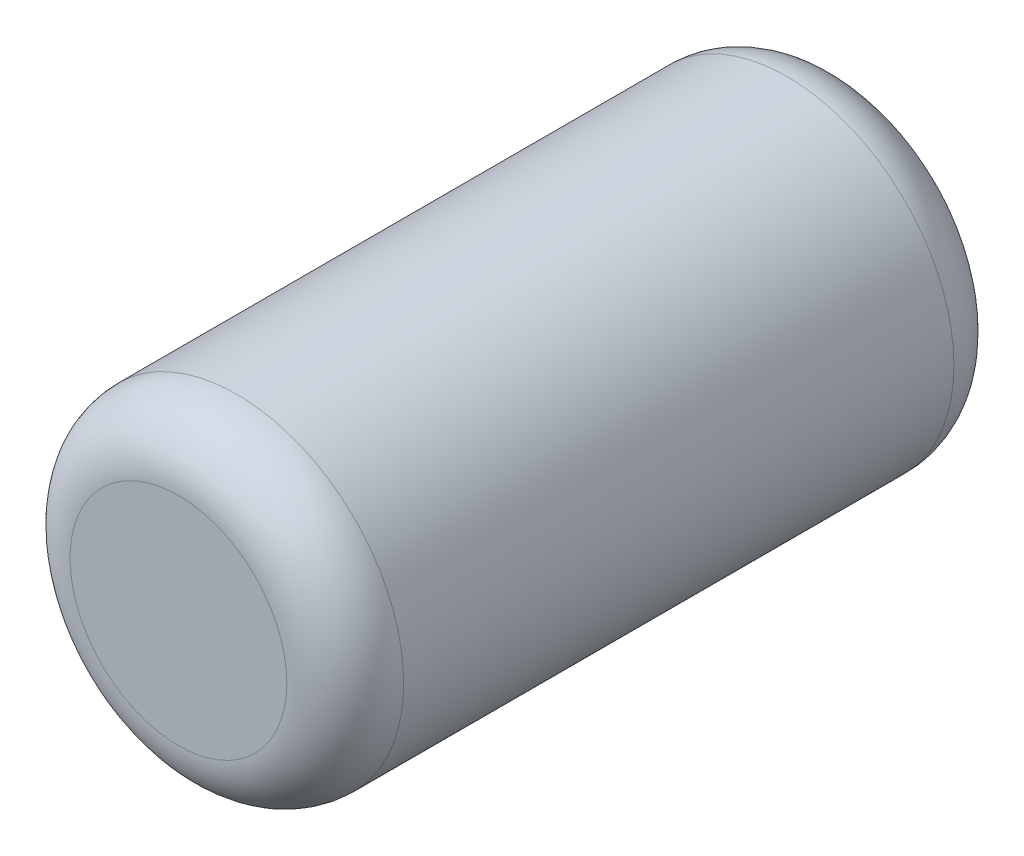
SolidWorks part; units mm, degrees
ref_plane "Front" through (0, 0, 0) normal (0, 0, 1) x (1, 0, 0)
ref_plane "Top" through (0, 0, 0) normal (0, 1, 0) x (1, 0, 0)
ref_plane "Right" through (0, 0, 0) normal (1, 0, 0) x (0, 0, -1)
sketch "Sketch1" plane through (0, 0, 0) normal (0, 0, 1) x (1, 0, 0)
  circle A0 centre (0, 0) radius 1
  dimension "D1" = 2
extrude "Boss-Extrude1" add sketch "Sketch1" along normal mid plane 4
fillet "Fillet1" radius 0.35 2 edges at (1, 0, -2) (1, 0, 2)
